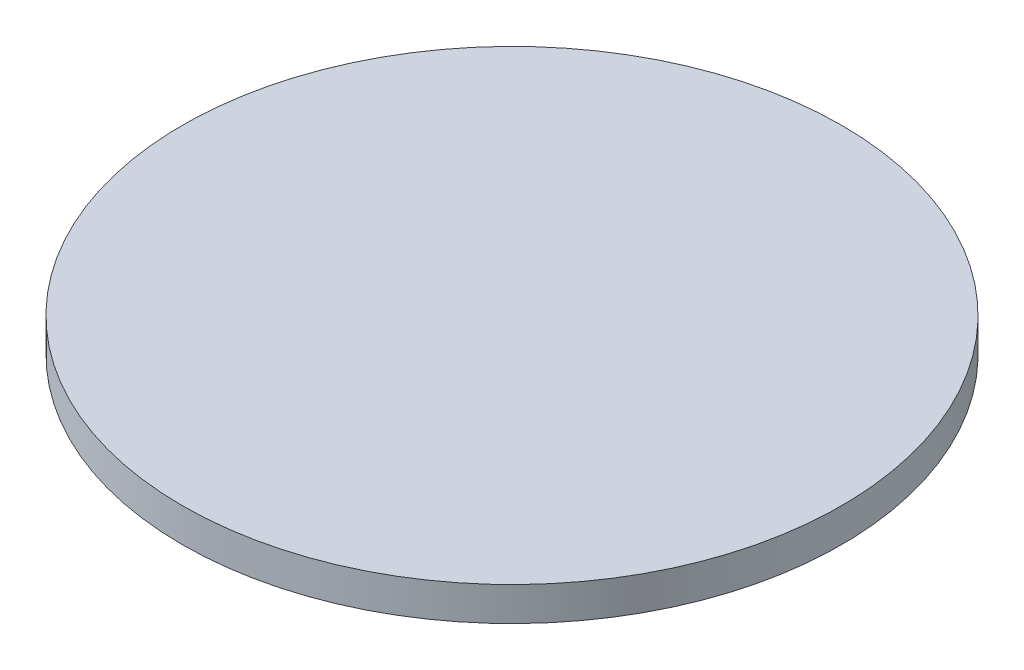
SolidWorks part; units mm, degrees
ref_plane "Front Plane" through (0, 0, 0) normal (0, 0, 1) x (1, 0, 0)
ref_plane "Top Plane" through (0, 0, 0) normal (0, 1, 0) x (1, 0, 0)
ref_plane "Right Plane" through (0, 0, 0) normal (1, 0, 0) x (0, 0, -1)
sketch "Sketch1" plane through (0, 0, 0) normal (0, 1, 0) x (1, 0, 0)
  circle A0 centre (0, 0) radius 19.5
  dimension "D1" = 39
extrude "Boss-Extrude1" add sketch "Sketch1" along normal blind 2
